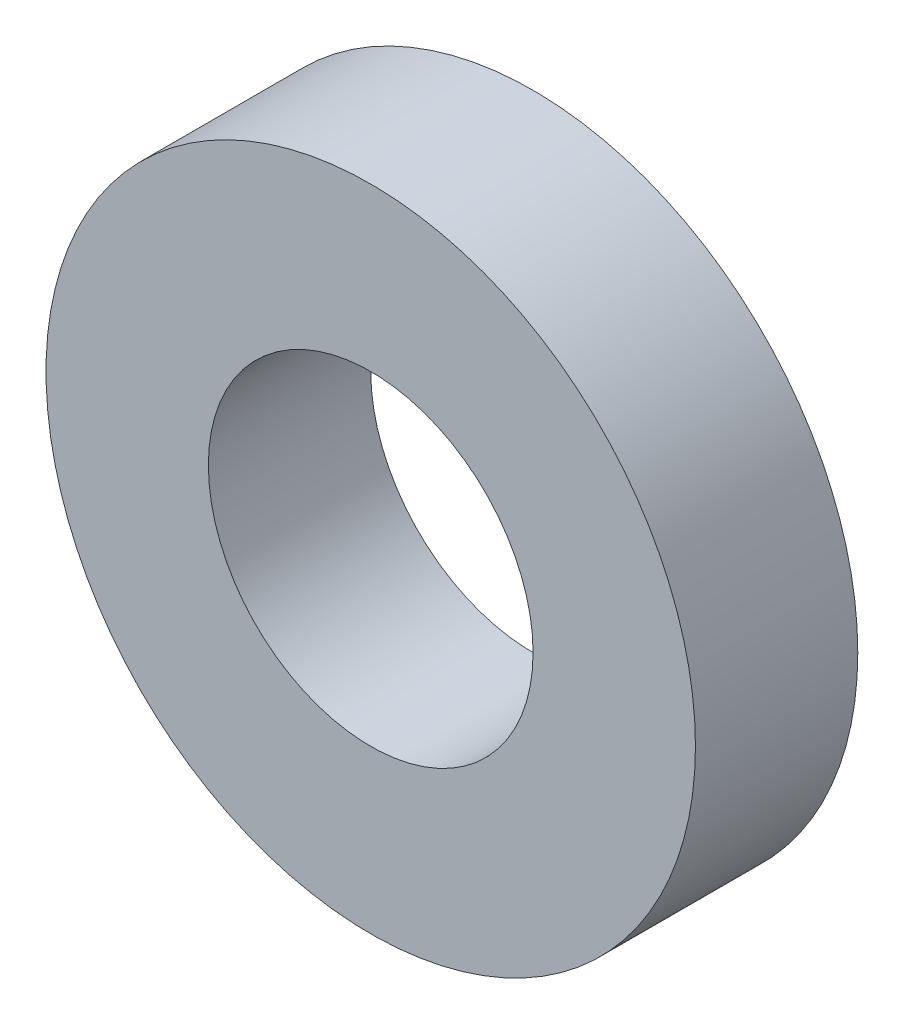
SolidWorks part; units mm, degrees
material "Latón"
ref_plane "Alzado" through (0, 0, 0) normal (0, 0, 1) x (1, 0, 0)
ref_plane "Planta" through (0, 0, 0) normal (0, 1, 0) x (1, 0, 0)
ref_plane "Vista lateral" through (0, 0, 0) normal (1, 0, 0) x (0, 0, -1)
sketch "Croquis1" plane through (0, 0, 0) normal (0, 1, 0) x (1, 0, 0)
  line L0 (0, 0) -> (0, 16.0323) construction
  line L1 (0.5, 0) -> (1, 0)
  line L2 (0.5, 0) -> (0.5, 0.5)
  line L3 (0.5, 0.5) -> (1, 0.5)
  line L4 (1, 0) -> (1, 0.5)
  dimension "D1" = 1
  dimension "D2" = 0.5
revolve "Revolución1" add sketch "Croquis1" angle 360 about L0
